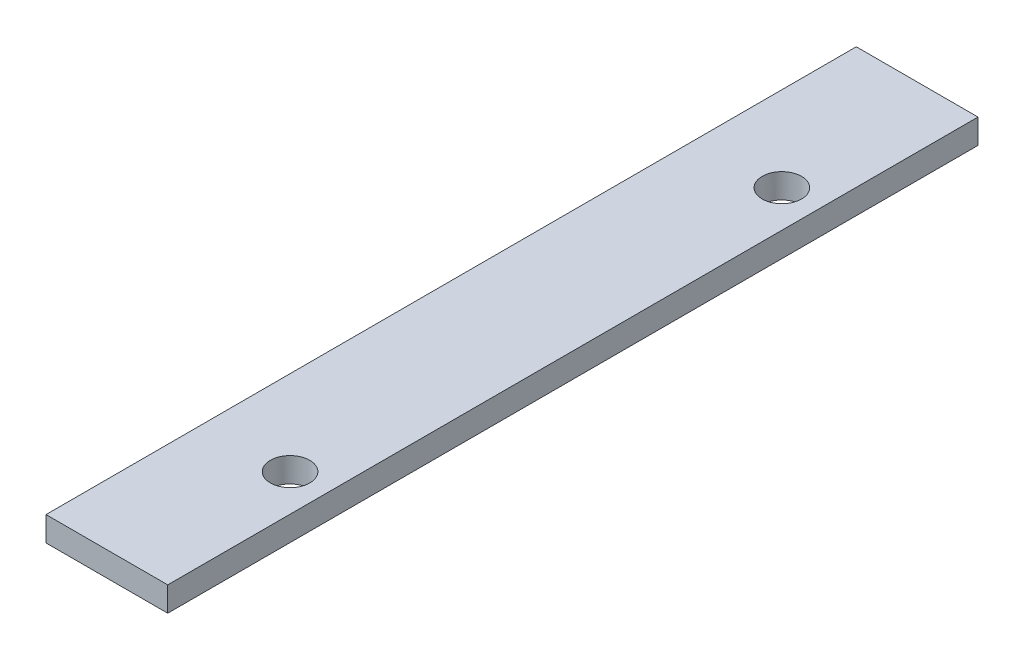
SolidWorks part; units mm, degrees
material "PET"
ref_plane "Спереди" through (0, 0, 0) normal (0, 0, 1) x (1, 0, 0)
ref_plane "Сверху" through (0, 0, 0) normal (0, 1, 0) x (1, 0, 0)
ref_plane "Справа" through (0, 0, 0) normal (1, 0, 0) x (0, 0, -1)
sketch "Эскиз1" plane through (0, 0, 0) normal (0, 1, 0) x (1, 0, 0)
  line L1 (4.95, 32.95) -> (-4.95, 32.95)
  line L2 (4.95, 32.95) -> (4.95, -32.95)
  line L3 (4.95, -32.95) -> (-4.95, -32.95)
  line L4 (-4.95, 32.95) -> (-4.95, -32.95)
  line L5 (4.95, 32.95) -> (-4.95, -32.95) construction
  line L6 (4.95, -32.95) -> (-4.95, 32.95) construction
  point P0 (0, 0)
  dimension "D1" = 9.9
  dimension "D2" = 65.9
extrude "Бобышка-Вытянуть1" add sketch "Эскиз1" along normal blind 2
sketch "Эскиз2" plane through (0, 2, 0) normal (0, 1, 0) x (1, 0, 0)
  line L0 (4.95, 0) -> (1.95, 0) construction
  line L1 (4.95, -32.95) -> (4.95, 32.95) construction
  line L2 (1.95, 20) -> (1.95, -20) construction
  circle A0 centre (1.95, 20) radius 1.6
  circle A1 centre (1.95, -20) radius 1.6
  point P8 (1.95, 0)
  dimension "D3" = 3.2
  dimension "D1" = 3
  dimension "D2" = 40
extrude "Вырез-Вытянуть1" cut sketch "Эскиз2" against normal through all both and the other way through all
